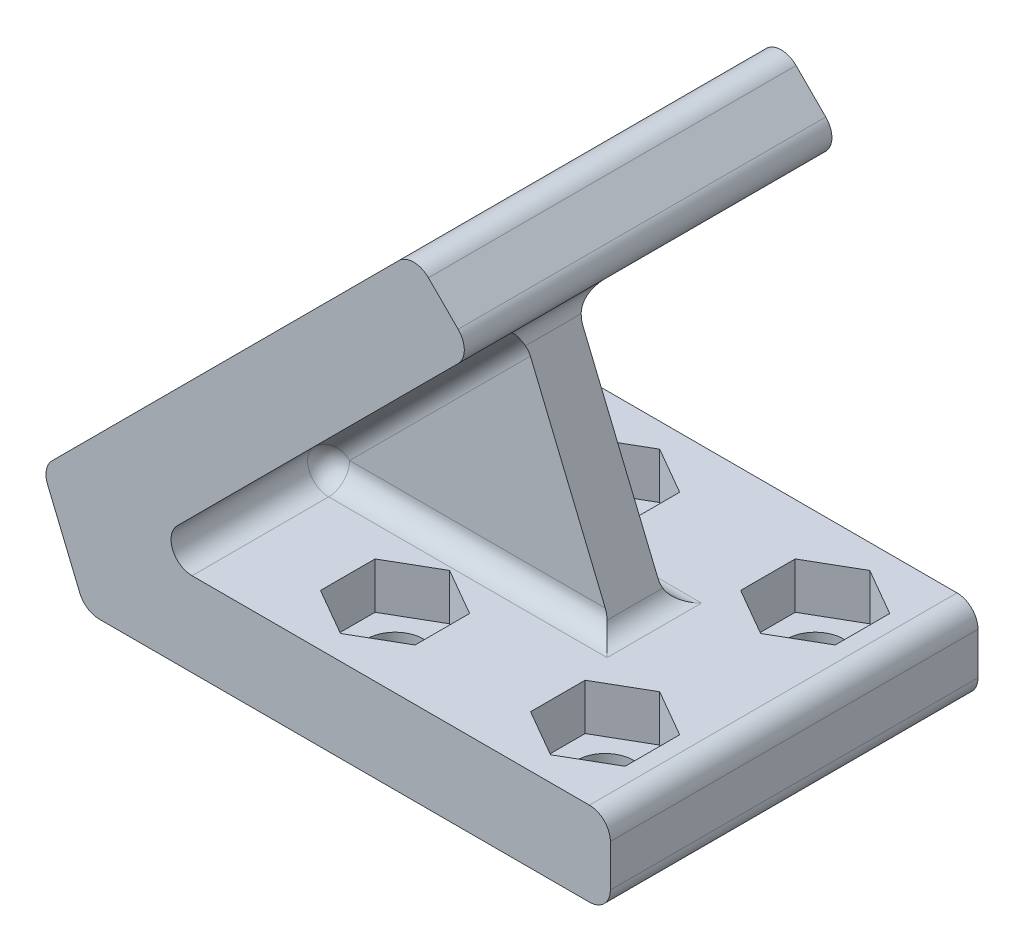
SolidWorks part; units mm, degrees
material "ABS"
ref_plane "Front Plane" through (0, 0, 0) normal (0, 0, 1) x (1, 0, 0)
ref_plane "Top Plane" through (0, 0, 0) normal (0, 1, 0) x (1, 0, 0)
ref_plane "Right Plane" through (0, 0, 0) normal (1, 0, 0) x (0, 0, -1)
sketch "Sketch1" plane through (0, 0, 0) normal (0, 0, 1) x (1, 0, 0)
  line L0 (0, 0) -> (63.5, 0)
  line L1 (63.5, 0) -> (63.5, 10.16)
  line L2 (63.5, 10.16) -> (6.7887, 10.16)
  line L3 (6.7887, 10.16) -> (46.8896, 50.2609)
  line L4 (46.8896, 50.2609) -> (39.7054, 57.4452)
  line L5 (39.7054, 57.4452) -> (-5.1958, 12.5439)
  line L6 (-5.1958, 12.5439) -> (0, 0)
  line L7 (6.7887, 10.16) -> (-2.5979, 6.2719) construction
  dimension "D1" = 45
  dimension "D2" = 10.16
  dimension "D3" = 63.5
  dimension "D4" = 10.16
extrude "Boss-Extrude1" add sketch "Sketch1" along normal blind 44.45 contours L0 L1 L2 L3 L4 L5 L6
sketch "Sketch2" plane through (0, 10.16, 0) normal (0, 1, 0) x (1, 0, 0)
  line L0 (27.94, -34.925) -> (53.34, -34.925) construction
  line L1 (53.34, -34.925) -> (53.34, -9.525) construction
  line L2 (53.34, -9.525) -> (27.94, -9.525) construction
  line L3 (27.94, -9.525) -> (27.94, -34.925) construction
  line L4 (40.64, -34.925) -> (40.64, -44.45) construction
  line L6 (40.64, -9.525) -> (40.64, 0) construction
  line L8 (63.5, -44.45) -> (63.5, 0) construction
  line L9 (63.5, 0) -> (6.7887, 0) construction
  line L10 (63.5, -44.45) -> (6.7887, -44.45) construction
  circle A0 centre (53.34, -34.925) radius 3.429
  circle A1 centre (53.34, -9.525) radius 3.429
  circle A2 centre (27.94, -9.525) radius 3.429
  circle A3 centre (27.94, -34.925) radius 3.429
  dimension "D2" = 6.858
  dimension "D1" = 25.4
  dimension "D3" = 10.16
extrude "Cut-Extrude1" cut sketch "Sketch2" against normal blind 44.45
sketch "Sketch3" plane through (-1.6857, 1.6857, 0) normal (0.7071, -0.7071, 0) x (0, 0, -1)
  line L0 (-34.925, 33.1358) -> (-9.525, 33.1358) construction
  line L1 (-9.525, 33.1358) -> (-9.525, 58.5358) construction
  line L2 (-9.525, 58.5358) -> (-34.925, 58.5358) construction
  line L3 (-34.925, 58.5358) -> (-34.925, 33.1358) construction
  line L4 (-44.45, 68.6958) -> (0, 68.6958) construction
  line L5 (-34.925, 45.8358) -> (-44.45, 45.8358) construction
  line L6 (-44.45, 11.9845) -> (-44.45, 68.6958) construction
  line L7 (-9.525, 45.8358) -> (0, 45.8358) construction
  line L8 (0, 11.9845) -> (0, 68.6958) construction
  circle A0 centre (-9.525, 33.1358) radius 3.429
  circle A1 centre (-9.525, 58.5358) radius 3.429
  circle A2 centre (-34.925, 58.5358) radius 3.429
  circle A3 centre (-34.925, 33.1358) radius 3.429
  dimension "D2" = 6.858
  dimension "D1" = 25.4
  dimension "D3" = 10.16
extrude "Cut-Extrude2" cut sketch "Sketch3" against normal blind 44.45
sketch "Sketch4" plane through (0, 10.16, 0) normal (0, 1, 0) x (1, 0, 0)
  line L0 (22.225, -31.6254) -> (22.225, -38.2246)
  line L1 (47.625, -31.6254) -> (47.625, -38.2246)
  line L2 (47.625, -38.2246) -> (53.34, -41.5241)
  line L3 (53.34, -41.5241) -> (59.055, -38.2246)
  line L4 (59.055, -38.2246) -> (59.055, -31.6254)
  line L5 (59.055, -31.6254) -> (53.34, -28.3259)
  line L6 (53.34, -28.3259) -> (47.625, -31.6254)
  line L7 (22.225, -38.2246) -> (27.94, -41.5241)
  line L8 (27.94, -41.5241) -> (33.655, -38.2246)
  line L9 (33.655, -38.2246) -> (33.655, -31.6254)
  line L10 (33.655, -31.6254) -> (27.94, -28.3259)
  line L11 (27.94, -28.3259) -> (22.225, -31.6254)
  line L12 (22.225, -6.2254) -> (22.225, -12.8246)
  line L13 (22.225, -12.8246) -> (27.94, -16.1241)
  line L14 (27.94, -16.1241) -> (33.655, -12.8246)
  line L15 (33.655, -12.8246) -> (33.655, -6.2254)
  line L16 (33.655, -6.2254) -> (27.94, -2.9259)
  line L17 (27.94, -2.9259) -> (22.225, -6.2254)
  line L18 (47.625, -6.2254) -> (47.625, -12.8246)
  line L19 (47.625, -12.8246) -> (53.34, -16.1241)
  line L20 (53.34, -16.1241) -> (59.055, -12.8246)
  line L21 (59.055, -12.8246) -> (59.055, -6.2254)
  line L22 (59.055, -6.2254) -> (53.34, -2.9259)
  line L23 (53.34, -2.9259) -> (47.625, -6.2254)
  circle A0 centre (53.34, -34.925) radius 5.715 construction
  circle A1 centre (27.94, -34.925) radius 5.715 construction
  circle A2 centre (27.94, -9.525) radius 5.715 construction
  circle A3 centre (53.34, -9.525) radius 5.715 construction
  circle A4 centre (53.34, -34.925) radius 3.429 construction
  dimension "D1" = 11.43
  dimension "D4" = 19.685
  dimension "D5" = 18.8009
  dimension "D2" = 2
  dimension "D3" = 2
extrude "Cut-Extrude3" cut sketch "Sketch4" against normal blind 5.588
sketch "Sketch5" plane through (-1.6857, 1.6857, 0) normal (0.7071, -0.7071, 0) x (0, 0, -1)
  line L0 (-2.9259, 58.5358) -> (-6.2254, 64.2508)
  line L1 (-28.3259, 58.5358) -> (-31.6254, 64.2508)
  line L2 (-31.6254, 64.2508) -> (-38.2246, 64.2508)
  line L3 (-38.2246, 64.2508) -> (-41.5241, 58.5358)
  line L4 (-41.5241, 58.5358) -> (-38.2246, 52.8208)
  line L5 (-38.2246, 52.8208) -> (-31.6254, 52.8208)
  line L6 (-31.6254, 52.8208) -> (-28.3259, 58.5358)
  line L7 (-6.2254, 64.2508) -> (-12.8246, 64.2508)
  line L8 (-12.8246, 64.2508) -> (-16.1241, 58.5358)
  line L9 (-16.1241, 58.5358) -> (-12.8246, 52.8208)
  line L10 (-12.8246, 52.8208) -> (-6.2254, 52.8208)
  line L11 (-6.2254, 52.8208) -> (-2.9259, 58.5358)
  line L12 (-2.9259, 33.1358) -> (-6.2254, 38.8508)
  line L13 (-6.2254, 38.8508) -> (-12.8246, 38.8508)
  line L14 (-12.8246, 38.8508) -> (-16.1241, 33.1358)
  line L15 (-16.1241, 33.1358) -> (-12.8246, 27.4208)
  line L16 (-12.8246, 27.4208) -> (-6.2254, 27.4208)
  line L17 (-6.2254, 27.4208) -> (-2.9259, 33.1358)
  line L18 (-28.3259, 33.1358) -> (-31.6254, 38.8508)
  line L19 (-31.6254, 38.8508) -> (-38.2246, 38.8508)
  line L20 (-38.2246, 38.8508) -> (-41.5241, 33.1358)
  line L21 (-41.5241, 33.1358) -> (-38.2246, 27.4208)
  line L22 (-38.2246, 27.4208) -> (-31.6254, 27.4208)
  line L23 (-31.6254, 27.4208) -> (-28.3259, 33.1358)
  circle A0 centre (-34.925, 58.5358) radius 5.715 construction
  circle A1 centre (-9.525, 58.5358) radius 5.715 construction
  circle A2 centre (-9.525, 33.1358) radius 5.715 construction
  circle A3 centre (-34.925, 33.1358) radius 5.715 construction
  circle A4 centre (-9.525, 33.1358) radius 3.429 construction
  dimension "D1" = 11.43
  dimension "D4" = 3.2996
  dimension "D5" = 5.715
  dimension "D2" = 2
  dimension "D3" = 2
extrude "Cut-Extrude4" cut sketch "Sketch5" against normal blind 5.588
ref_plane "Plane1" through (0, 0, 22.225) normal (0, 0, 1) x (1, 0, 0)
sketch "Sketch6" plane through (0, 0, 22.225) normal (0, 0, 1) x (1, 0, 0)
  line L0 (6.7887, 10.16) -> (33.7295, 37.1008)
  line L1 (33.7295, 37.1008) -> (44.8887, 10.16)
  line L2 (44.8887, 10.16) -> (6.7887, 10.16)
  dimension "D1" = 45
  dimension "D2" = 38.1
extrude "Boss-Extrude2" add sketch "Sketch6" along normal mid plane 6.35
fillet "Fillet1" radius 2.54 14 edges at (6.7887, 10.16, 9.525) (0, 0, 22.225) (-5.1958, 12.5439, 22.225) (46.8896, 50.2609, 22.225) (39.7054, 57.4452, 22.225) (63.5, 0, 22.225) (63.5, 10.16, 22.225) (25.8387, 10.16, 19.05) (20.2591, 23.6304, 19.05) (33.7295, 37.1008, 22.225) (44.8887, 10.16, 22.225) (25.8387, 10.16, 25.4) (20.2591, 23.6304, 25.4) (6.7887, 10.16, 34.925)
